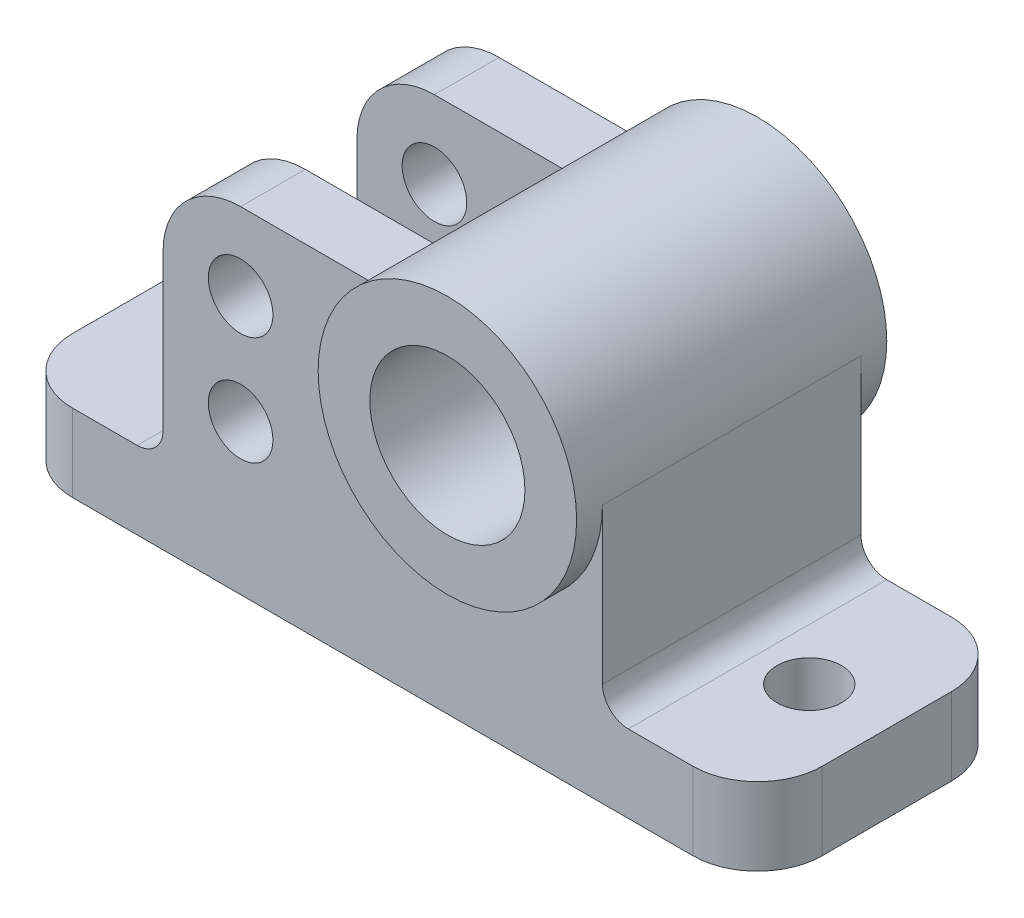
SolidWorks part; units mm, degrees
material "AISI 304"
ref_plane "Front Plane" through (0, 0, 0) normal (0, 0, 1) x (1, 0, 0)
ref_plane "Top Plane" through (0, 0, 0) normal (0, 1, 0) x (1, 0, 0)
ref_plane "Right Plane" through (0, 0, 0) normal (1, 0, 0) x (0, 0, -1)
sketch "Sketch1" plane through (0, 0, 0) normal (0, 0, 1) x (1, 0, 0)
  line L0 (0, 0) -> (290, 0)
  line L1 (290, 0) -> (290, 30)
  line L2 (290, 30) -> (230, 30)
  line L3 (0, 0) -> (0, 30)
  line L4 (0, 30) -> (60, 30)
  line L5 (60, 30) -> (60, 130)
  line L6 (60, 130) -> (230, 130)
  line L7 (230, 130) -> (230, 30)
  dimension "D1" = 290
  dimension "D2" = 30
  dimension "D3" = 60
  dimension "D4" = 100
  dimension "D5" = 170
extrude "Boss-Extrude1" add sketch "Sketch1" along normal mid plane 100
fillet "Fillet1" radius 30 2 edges at (230, 130, 0) (60, 130, 0)
sketch "Sketch2" plane through (0, 0, 0) normal (0, 0, 1) x (1, 0, 0)
  line L1 (230, 30) -> (230, 100) construction
  line L2 (290, 30) -> (230, 30) construction
  circle A0 centre (180, 100) radius 50
  dimension "D1" = 100
  dimension "D2" = 70
  dimension "D3" = 50
extrude "Boss-Extrude2" add sketch "Sketch2" along normal mid plane 120
sketch "Sketch3" plane through (0, 0, 60) normal (0, 0, 1) x (1, 0, 0)
  circle A0 centre (180, 100) radius 30
  dimension "D1" = 60
extrude "Cut-Extrude1" cut sketch "Sketch3" against normal through all
fillet "Fillet2" radius 10 2 edges at (60, 30, 0) (230, 30, 0)
sketch "Sketch5" plane through (0, 0, 0) normal (0, 0, 1) x (1, 0, 0)
  line L0 (140, 130) -> (60, 130)
  line L1 (140, 130) -> (90, 130) construction
  line L2 (60, 40) -> (60, 130)
  line L3 (60, 100) -> (60, 40) construction
  line L4 (130, 100) -> (130, 40)
  line L5 (130, 40) -> (60, 40)
  circle A0 centre (180, 100) radius 50 construction
  arc A1 (140, 130) -> (130, 100) centre (180, 100) ccw
  dimension "D1" = 90
extrude "Cut-Extrude2" cut sketch "Sketch5" against normal mid plane 50
sketch "Sketch6" plane through (0, 0, 50) normal (0, 0, 1) x (1, 0, 0)
  circle A0 centre (90, 100) radius 12.5
  circle A1 centre (90, 58) radius 12.5
  dimension "D1" = 25
  dimension "D2" = 42
extrude "Cut-Extrude3" cut sketch "Sketch6" against normal through all
fillet "Fillet3" radius 25 4 edges at (290, 15, -50) (290, 15, 50) (0, 15, -50) (0, 15, 50)
sketch "Sketch10" plane through (0, 30, 0) normal (0, 1, 0) x (1, 0, 0)
  line L0 (0, -25) -> (0, 25) construction
  line L1 (290, -25) -> (290, 25) construction
  circle A0 centre (30, 0) radius 12.5
  circle A1 centre (260, 0) radius 12.5
  dimension "D1" = 25
  dimension "D2" = 30
  dimension "D3" = 30
extrude "Cut-Extrude5" cut sketch "Sketch10" against normal through all
